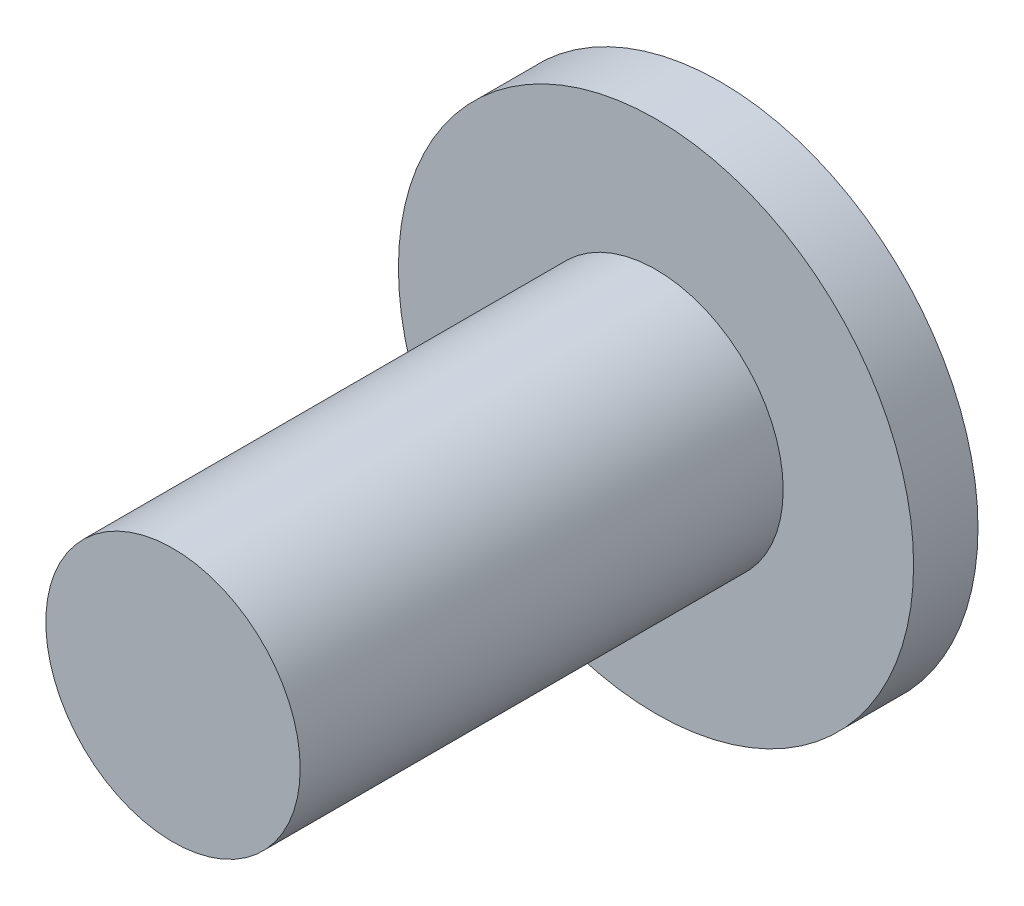
SolidWorks part; units mm, degrees
ref_plane "Front Plane" through (0, 0, 0) normal (0, 0, 1) x (1, 0, 0)
ref_plane "Top Plane" through (0, 0, 0) normal (0, 1, 0) x (1, 0, 0)
ref_plane "Right Plane" through (0, 0, 0) normal (1, 0, 0) x (0, 0, -1)
sketch "Sketch1" plane through (0, 0, 0) normal (0, 1, 0) x (1, 0, 0)
  line L0 (0, 0) -> (0, 15)
  line L1 (0, 15) -> (0, 17)
  line L2 (0, 17) -> (8, 17)
  line L3 (8, 17) -> (8, 15)
  line L4 (8, 15) -> (0, 15)
  line L5 (3.95, 15) -> (3.95, 0)
  line L6 (3.95, 0) -> (0, 0)
  dimension "D1" = 15
  dimension "D2" = 8
  dimension "D3" = 2
  dimension "D4" = 3.95
  dimension "D5" = 3.95
revolve "Revolve1" add sketch "Sketch1" angle 360 about L0
